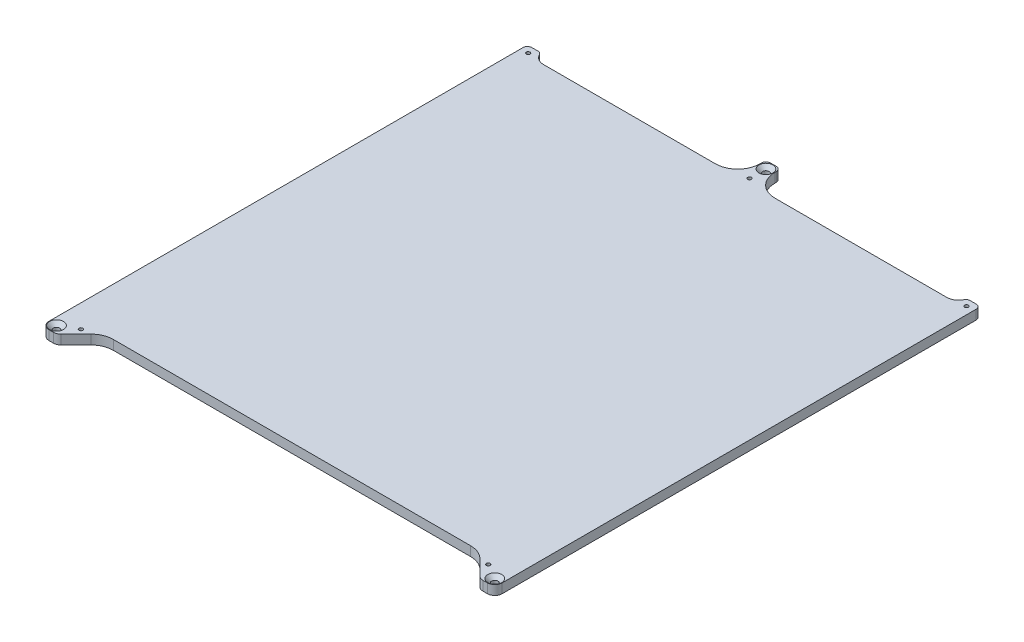
SolidWorks part; units mm, degrees
ref_plane "Front Plane" through (0, 0, 0) normal (0, 0, 1) x (1, 0, 0)
ref_plane "Top Plane" through (0, 0, 0) normal (0, 1, 0) x (1, 0, 0)
ref_plane "Right Plane" through (0, 0, 0) normal (1, 0, 0) x (0, 0, -1)
ref_plane "Plane1" through (0, 6.35, 0) normal (0, 1, 0) x (1, 0, 0)
sketch "Sketch1" plane through (0, 6.35, 0) normal (0, 1, 0) x (1, 0, 0)
  line L0 (152.5, 158.5) -> (-152.5, 158.5)
  line L1 (-152.5, 158.5) -> (-152.5, -168.5)
  line L2 (-152.5, -168.5) -> (152.5, -168.5)
  line L3 (152.5, -168.5) -> (152.5, 158.5)
extrude "Boss-Extrude1" add sketch "Sketch1" against normal blind 6.35
sketch "Sketch2" plane through (0, 6.35, 0) normal (0, 1, 0) x (-1, 0, 0)
  line L0 (-143.448, -158.5) -> (143.448, -158.5)
  line L1 (135.702, -152.5) -> (-135.702, -152.5)
  arc A0 (143.448, -158.5) -> (135.702, -152.5) centre (135.702, -160.5) ccw
  arc A1 (-135.702, -152.5) -> (-143.448, -158.5) centre (-135.702, -160.5) ccw
extrude "Cut-Extrude1" cut sketch "Sketch2" against normal through all
sketch "Sketch3" plane through (0, 0, -152.5) normal (0, 0, -1) x (-1, 0, 0)
  line L0 (5, 0) -> (-5, 0)
  line L1 (-5, 0) -> (-5, 6.35)
  line L2 (-5, 6.35) -> (5, 6.35)
  line L3 (5, 6.35) -> (5, 0)
extrude "Boss-Extrude2" add sketch "Sketch3" along normal blind 19
sketch "Sketch4" plane through (0, 0, 0) normal (0, -1, 0) x (1, 0, 0)
  line L0 (-126.5, 168.5) -> (-126.5, 152.5)
  line L1 (-126.5, 152.5) -> (126.5, 152.5)
  line L2 (126.5, 152.5) -> (126.5, 168.5)
  line L3 (126.5, 168.5) -> (-126.5, 168.5)
extrude "Cut-Extrude2" cut sketch "Sketch4" against normal through all
draft "Draft1" type of draft neutral plane draft angle 45 faces to draft 2 face at (-126.5, 3.175, 160.5) face at (126.5, 3.175, 160.5) neutral plane through (-126.5, 6.35, 152.5) neutral plane normal (0, 0, 1) parameters "D1"=45
hole_wizard "Ø4.3 (4.3) Diameter Hole1" positions "Sketch6" profile "Sketch5" hole size "Ø4.3" standard "ANSI Metric" end condition through all
sketch "Sketch6" plane through (0, 6.35, 0) normal (0, 1, 0) x (1, 0, 0)
  point P0 (0, 166.5)
  point P1 (-147.5, -163.5)
  point P2 (147.5, -163.5)
sketch "Sketch5" plane through (0, 6.35, -166.5) normal (1, 0, 0) x (0, 0, 1)
  line L0 (0, 0) -> (0, 6.35)
  line L1 (0, 6.35) -> (2.15, 6.35)
  line L2 (2.15, 6.35) -> (2.15, 0)
  line L5 (2.15, 0) -> (0, 0)
  line L11 (0, -6.35) -> (0, 107.95) construction
  dimension "Thru Hole Dia." = 4.3
  dimension "Thru Hole Depth" = 6.35
hole_wizard "Ø2.5 (2.5) Diameter Hole1" positions "Sketch8" profile "Sketch7" hole size "Ø2.5" standard "ANSI Metric"
sketch "Sketch8" plane through (0, 0, 0) normal (0, -1, 0) x (-1, 0, 0)
  point P0 (147.5, 154)
  point P1 (-147.5, 154)
  point P2 (-137.1077, -157.5)
  point P3 (137.1077, -157.5)
  point P4 (0, 155.5)
sketch "Sketch7" plane through (-147.5, 0, -154) normal (1, 0, 0) x (0, 0, -1)
  line L0 (0, 0) -> (0, 6.35)
  line L1 (0, 6.35) -> (1.25, 6.35)
  line L2 (1.25, 6.35) -> (1.25, 0)
  line L5 (1.25, 0) -> (0, 0)
  line L11 (0, -6.35) -> (0, 107.95) construction
  dimension "Thru Hole Dia." = 2.5
  dimension "Thru Hole Depth" = 6.35
chamfer "Chamfer1" distance 2.55 angle 45 3 edges at (-147.5, 6.35, 165.65) (0, 6.35, -164.35) (147.5, 6.35, 165.65)
fillet "Fillet1" radius 3 6 edges at (143.448, 3.175, -158.5) (-152.5, 3.175, -158.5) (152.5, 3.175, -158.5) (-5, 3.175, -171.5) (5, 3.175, -171.5) (-143.448, 3.175, -158.5)
fillet "Fillet2" radius 5 4 edges at (-142.5, 3.175, 168.5) (-152.5, 3.175, 168.5) (152.5, 3.175, 168.5) (142.5, 3.175, 168.5)
fillet "Fillet3" radius 15 4 edges at (5, 3.175, -152.5) (-5, 3.175, -152.5) (126.5, 3.175, 152.5) (-126.5, 3.175, 152.5)
